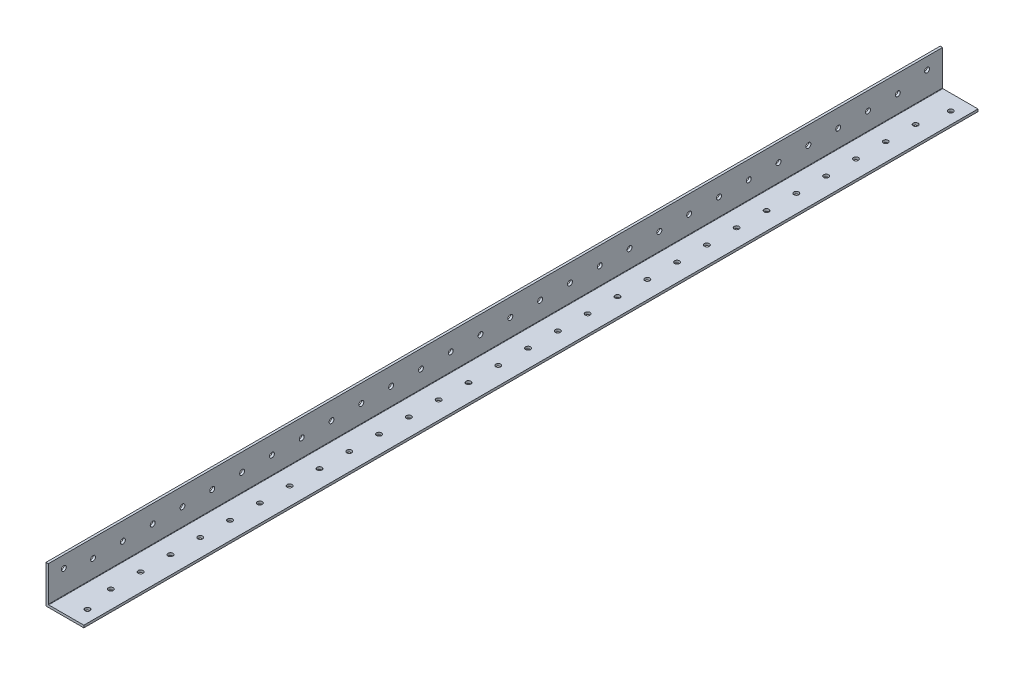
SolidWorks part; units mm, degrees
ref_plane "Front Plane" through (0, 0, 0) normal (0, 0, 1) x (1, 0, 0)
ref_plane "Top Plane" through (0, 0, 0) normal (0, 1, 0) x (1, 0, 0)
ref_plane "Right Plane" through (0, 0, 0) normal (1, 0, 0) x (0, 0, -1)
sketch "Sketch1" plane through (0, 0, 0) normal (0, 0, 1) x (1, 0, 0)
  line L0 (0, 25.4) -> (0, 0) construction
  line L1 (0, 0) -> (25.4, 0) construction
  line L2 (25.4, 0) -> (25.4, 1.5875) construction
  line L3 (25.4, 1.5875) -> (1.5875, 1.5875) construction
  line L4 (1.5875, 1.5875) -> (1.5875, 25.4) construction
  line L6 (1.5875, 25.4) -> (0, 25.4) construction
  arc A0 (1.5875, 1.8415) -> (1.8415, 1.5875) centre (1.8415, 1.8415) ccw construction
  point P4 (0, 0)
  dimension "Inside Corner Radius" = 0.254
  dimension "Outside Height" = 25.4
  dimension "Inside Height" = 23.8125
  dimension "Outside Width" = 25.4
  dimension "Inside Width" = 23.8125
  dimension "Wall Thickness" = 1.5875
  dimension "Shape" = 90
sketch "Sketch2" plane through (0, 0, 0) normal (1, 0, 0) x (0, 0, -1)
  line L0 (1219.2, 0) -> (-1219.2, 0) construction
  line L1 (-1219.2, 25.4) -> (-1219.2, 0) construction
  line L2 (1219.2, 25.4) -> (1219.2, 0) construction
  point P0 (-1189.99, 0)
  point P4 (0, 0)
  point P6 (1189.99, 0)
  dimension "D1" = 29.21
  dimension "D2" = 29.21
  dimension "D3" = 25.4
  dimension "Length" = 2438.4
sketch "Sketch3" plane through (0, 0, 0) normal (0, 0, 1) x (1, 0, 0)
  line L0 (1.5875, 25.4) -> (0, 25.4)
  line L1 (0, 25.4) -> (0, 0)
  line L2 (0, 0) -> (25.4, 0)
  line L3 (25.4, 0) -> (25.4, 1.5875)
  line L4 (25.4, 1.5875) -> (1.5875, 1.5875)
  line L5 (1.5875, 1.5875) -> (1.5875, 25.4)
extrude "Boss-Extrude1" add sketch "Sketch3" along normal mid plane 2438.4
fillet "Fillet1" radius 0.254 1 edges at (1.5875, 1.5875, 0)
sketch "Sketch4" plane through (0, 0, 0) normal (-1, 0, 0) x (0, 0, 1)
  line L0 (1219.2, 25.4) -> (1219.2, 0) construction
  line L1 (-1219.2, 0) -> (619.2, 0)
  line L2 (-1219.2, 0) -> (-1219.2, 74.9453)
  line L3 (-1219.2, 74.9453) -> (619.2, 74.9453)
  line L4 (619.2, 0) -> (619.2, 74.9453)
  dimension "D1" = 600
extrude "Cut-Extrude1" cut sketch "Sketch4" against normal blind 60
sketch "Sketch5" plane through (1.5875, 0, 0) normal (1, 0, 0) x (0, 0, -1)
  line L0 (-1189.2, 25.4) -> (-1189.2, 1.5875) construction
  line L1 (-1219.2, 25.4) -> (-619.2, 25.4) construction
  line L2 (-1219.2, 1.5875) -> (-619.2, 1.5875) construction
  line L3 (-1208.8241, 17.4625) -> (-1189.2, 17.4625) construction
  line L4 (-629.5759, 17.4625) -> (-629.5759, 3.8186) construction
  line L5 (-623.0735, 3.8186) -> (-633.4875, 3.8186) construction
  line L6 (-649.2, 13.4937) -> (-629.5759, 13.4937) construction
  circle A0 centre (-629.5759, 17.4625) radius 1.65
  circle A1 centre (-1208.8241, 17.4625) radius 1.65
  circle A2 centre (-1189.2, 13.4937) radius 1.65
  circle A3 centre (-1169.2, 13.4937) radius 1.65
  circle A4 centre (-1149.2, 13.4937) radius 1.65
  circle A5 centre (-1129.2, 13.4937) radius 1.65
  circle A6 centre (-1109.2, 13.4937) radius 1.65
  circle A7 centre (-1089.2, 13.4937) radius 1.65
  circle A8 centre (-1069.2, 13.4937) radius 1.65
  circle A9 centre (-1049.2, 13.4937) radius 1.65
  circle A10 centre (-1029.2, 13.4937) radius 1.65
  circle A11 centre (-1009.2, 13.4937) radius 1.65
  circle A12 centre (-989.2, 13.4937) radius 1.65
  circle A13 centre (-969.2, 13.4937) radius 1.65
  circle A14 centre (-949.2, 13.4937) radius 1.65
  circle A15 centre (-929.2, 13.4937) radius 1.65
  circle A16 centre (-909.2, 13.4937) radius 1.65
  circle A17 centre (-889.2, 13.4937) radius 1.65
  circle A18 centre (-869.2, 13.4937) radius 1.65
  circle A19 centre (-849.2, 13.4937) radius 1.65
  circle A20 centre (-829.2, 13.4937) radius 1.65
  circle A21 centre (-809.2, 13.4937) radius 1.65
  circle A22 centre (-789.2, 13.4937) radius 1.65
  circle A23 centre (-769.2, 13.4937) radius 1.65
  circle A24 centre (-749.2, 13.4937) radius 1.65
  circle A25 centre (-729.2, 13.4937) radius 1.65
  circle A26 centre (-709.2, 13.4937) radius 1.65
  circle A27 centre (-689.2, 13.4937) radius 1.65
  circle A28 centre (-669.2, 13.4937) radius 1.65
  circle A29 centre (-649.2, 13.4937) radius 1.65
  dimension "D1" = 3.3
  dimension "D2" = 20
extrude "Cut-Extrude2" cut sketch "Sketch5" against normal blind 60
sketch "Sketch6" plane through (0, 1.5875, 0) normal (0, 1, 0) x (1, 0, 0)
  line L0 (25.4, -649.2) -> (1.5875, -649.2) construction
  line L1 (25.4, -1219.2) -> (25.4, -619.2) construction
  line L2 (1.5875, -1219.2) -> (1.5875, -619.2) construction
  line L3 (17.4625, -629.5759) -> (17.4625, -649.2) construction
  line L4 (17.4625, -1208.8241) -> (3.8186, -1208.8241) construction
  line L5 (3.8186, -1215.3265) -> (3.8186, -1204.9125) construction
  line L6 (13.4937, -1189.2) -> (13.4937, -1208.8241) construction
  circle A0 centre (17.4625, -629.5759) radius 1.65
  circle A1 centre (17.4625, -1208.8241) radius 1.65
  circle A2 centre (13.4937, -649.2) radius 1.65
  circle A3 centre (13.4937, -669.2) radius 1.65
  circle A4 centre (13.4937, -689.2) radius 1.65
  circle A5 centre (13.4937, -709.2) radius 1.65
  circle A6 centre (13.4937, -729.2) radius 1.65
  circle A7 centre (13.4937, -749.2) radius 1.65
  circle A8 centre (13.4937, -769.2) radius 1.65
  circle A9 centre (13.4937, -789.2) radius 1.65
  circle A10 centre (13.4937, -809.2) radius 1.65
  circle A11 centre (13.4937, -829.2) radius 1.65
  circle A12 centre (13.4937, -849.2) radius 1.65
  circle A13 centre (13.4937, -869.2) radius 1.65
  circle A14 centre (13.4937, -889.2) radius 1.65
  circle A15 centre (13.4937, -909.2) radius 1.65
  circle A16 centre (13.4937, -929.2) radius 1.65
  circle A17 centre (13.4937, -949.2) radius 1.65
  circle A18 centre (13.4937, -969.2) radius 1.65
  circle A19 centre (13.4937, -989.2) radius 1.65
  circle A20 centre (13.4937, -1009.2) radius 1.65
  circle A21 centre (13.4937, -1029.2) radius 1.65
  circle A22 centre (13.4937, -1049.2) radius 1.65
  circle A23 centre (13.4937, -1069.2) radius 1.65
  circle A24 centre (13.4937, -1089.2) radius 1.65
  circle A25 centre (13.4937, -1109.2) radius 1.65
  circle A26 centre (13.4937, -1129.2) radius 1.65
  circle A27 centre (13.4937, -1149.2) radius 1.65
  circle A28 centre (13.4937, -1169.2) radius 1.65
  circle A29 centre (13.4937, -1189.2) radius 1.65
  dimension "D1" = 3.3
  dimension "D3" = 20
  dimension "D2" = 28
extrude "Cut-Extrude3" cut sketch "Sketch6" against normal blind 60
equation "\"D1@Boss-Extrude1\"=\"Length@Sketch2\""
equation "\"D1@Sketch2\" = \"Outside Width@Sketch1\" * 1.15"
equation "\"D2@Sketch2\"=\"D1@Sketch2\""
equation "\"D1@Fillet1\"=\"Inside Corner Radius@Sketch1\""
equation "\"D3@Sketch2\"=\"Outside Height@Sketch1\""
